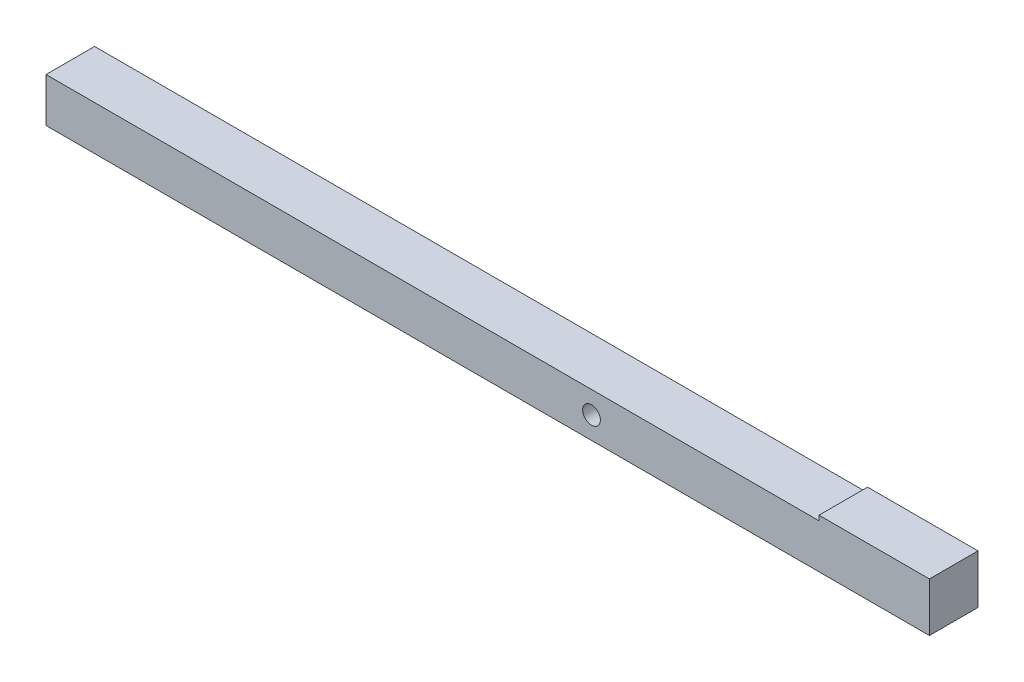
SolidWorks part; units mm, degrees
material "Balsa"
ref_plane "Front Plane" through (0, 0, 0) normal (0, 0, 1) x (1, 0, 0)
ref_plane "Top Plane" through (0, 0, 0) normal (0, 1, 0) x (1, 0, 0)
ref_plane "Right Plane" through (0, 0, 0) normal (1, 0, 0) x (0, 0, -1)
sketch "Sketch1" plane through (0, 0, 0) normal (1, 0, 0) x (0, 0, -1)
  line L1 (-11, -10) -> (11, -10)
  line L2 (-11, -10) -> (-11, 10)
  line L3 (-11, 10) -> (11, 10)
  line L4 (11, -10) -> (11, 10)
  line L5 (-11, -10) -> (11, 10) construction
  line L6 (-11, 10) -> (11, -10) construction
  point P0 (0, 0)
  dimension "D1" = 22
  dimension "D2" = 20
extrude "Boss-Extrude1" add sketch "Sketch1" along normal blind 400
sketch "Sketch2" plane through (0, 0, 11) normal (0, 0, 1) x (1, 0, 0)
  line L0 (247, 10) -> (247, -10) construction
  line L1 (400, 10) -> (0, 10) construction
  line L2 (400, -10) -> (0, -10) construction
  line L3 (0, 10) -> (0, -10) construction
  circle A0 centre (247, 0) radius 4
  dimension "D1" = 8
  dimension "D2" = 247
extrude "Cut-Extrude1" cut sketch "Sketch2" against normal through all
sketch "Sketch3" plane through (0, 10, 0) normal (0, 1, 0) x (1, 0, 0)
  line L0 (400, -11) -> (0, -11) construction
  line L1 (400, 11) -> (350, 11)
  line L2 (400, 11) -> (400, -11)
  line L3 (400, -11) -> (350, -11)
  line L4 (350, 11) -> (350, -11)
  dimension "D1" = 50
extrude "Boss-Extrude2" add sketch "Sketch3" along normal blind 2.2
